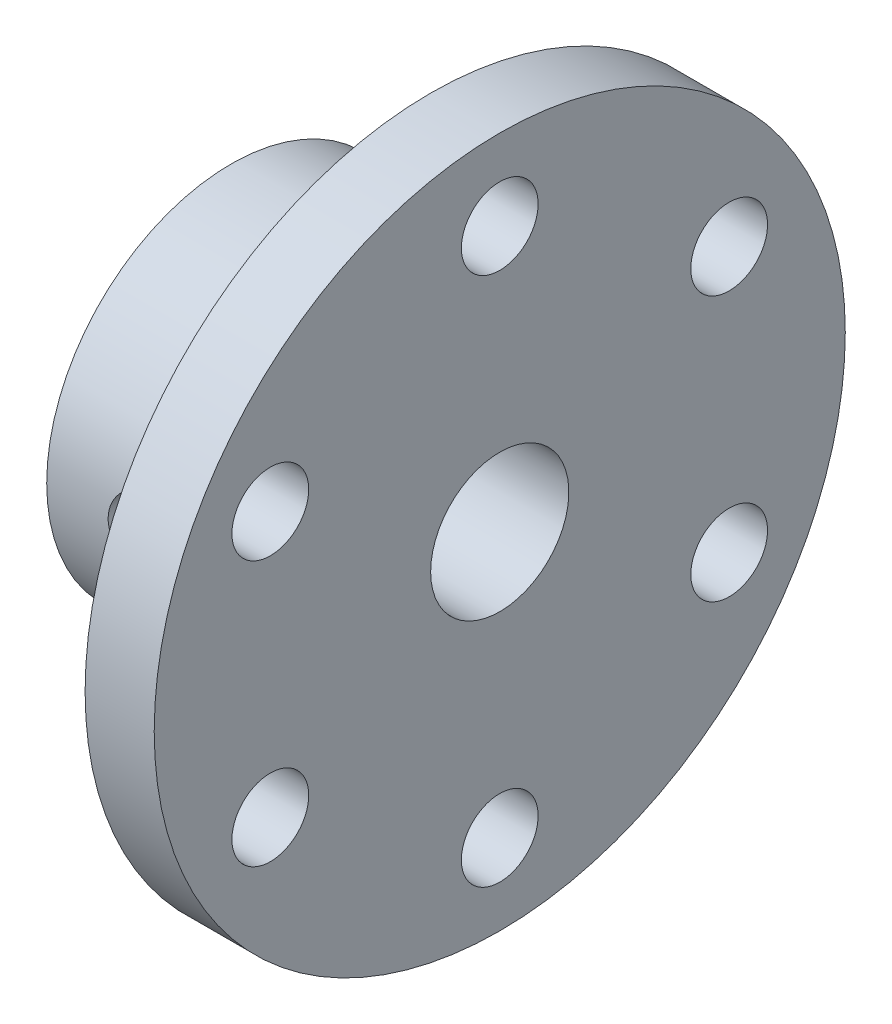
SolidWorks part; units mm, degrees
ref_plane "Front Plane" through (0, 0, 0) normal (0, 0, 1) x (1, 0, 0)
ref_plane "Top Plane" through (0, 0, 0) normal (0, 1, 0) x (1, 0, 0)
ref_plane "Right Plane" through (0, 0, 0) normal (1, 0, 0) x (0, 0, -1)
sketch "Sketch1" plane through (0, 0, 0) normal (0, 0, 1) x (1, 0, 0)
  line L0 (-11.6129, 0) -> (15.7189, 0) construction
  line L1 (-14.7005, 4.5) -> (-14.7005, 12)
  line L2 (-14.7005, 12) -> (-1.7005, 12)
  line L3 (-1.7005, 12) -> (-1.7005, 22.5)
  line L4 (-1.7005, 22.5) -> (2.7995, 22.5)
  line L5 (2.7995, 22.5) -> (2.7995, 4.5)
  line L6 (2.7995, 4.5) -> (-14.7005, 4.5)
  dimension "D1" = 4.5
  dimension "D2" = 4.5
  dimension "D3" = 13
  dimension "D4" = 22.5
  dimension "D5" = 12
revolve "Revolve1" add sketch "Sketch1" angle 360 about L0
sketch "Sketch2" plane through (-1.7005, 0, 0) normal (-1, 0, 0) x (0, 0, 1)
  line L0 (0, -17.25) -> (0, 17.25) construction
  line L1 (-14.9389, 8.625) -> (14.9389, -8.625) construction
  line L2 (14.9389, 8.625) -> (-14.9389, -8.625) construction
  circle A0 centre (0, 0) radius 17.25 construction
  circle A9 centre (0, 17.25) radius 2.5
  circle A10 centre (14.9389, 8.625) radius 2.5
  circle A11 centre (14.9389, -8.625) radius 2.5
  circle A12 centre (0, -17.25) radius 2.5
  circle A13 centre (-14.9389, -8.625) radius 2.5
  circle A14 centre (-14.9389, 8.625) radius 2.5
  point P22 (0, 0)
  dimension "D1" = 34.5
  dimension "D2" = 60
  dimension "D4" = 5
  dimension "D3" = 60
  dimension "D5" = 6
extrude "Cut-Extrude1" cut sketch "Sketch2" against normal up to surface (4.5 mm away) up to face at (2.7995, 0, 22.5)
ref_plane "Plane1" through (0, 0, 12) normal (0, 0, 1) x (1, 0, 0)
sketch "Sketch3" plane through (0, 0, 12) normal (0, 0, 1) x (1, 0, 0)
  line L0 (-14.7005, 0) -> (-1.7005, 0) construction
  line L1 (-14.7005, 12) -> (-14.7005, -12) construction
  line L2 (-1.7005, 22.5) -> (-1.7005, -22.5) construction
  circle A0 centre (-8.2005, 0) radius 2.5
  dimension "D1" = 5
extrude "Cut-Extrude2" cut sketch "Sketch3" against normal up to surface (7.5 mm away) up to face at (2.7995, 0, 4.5)
